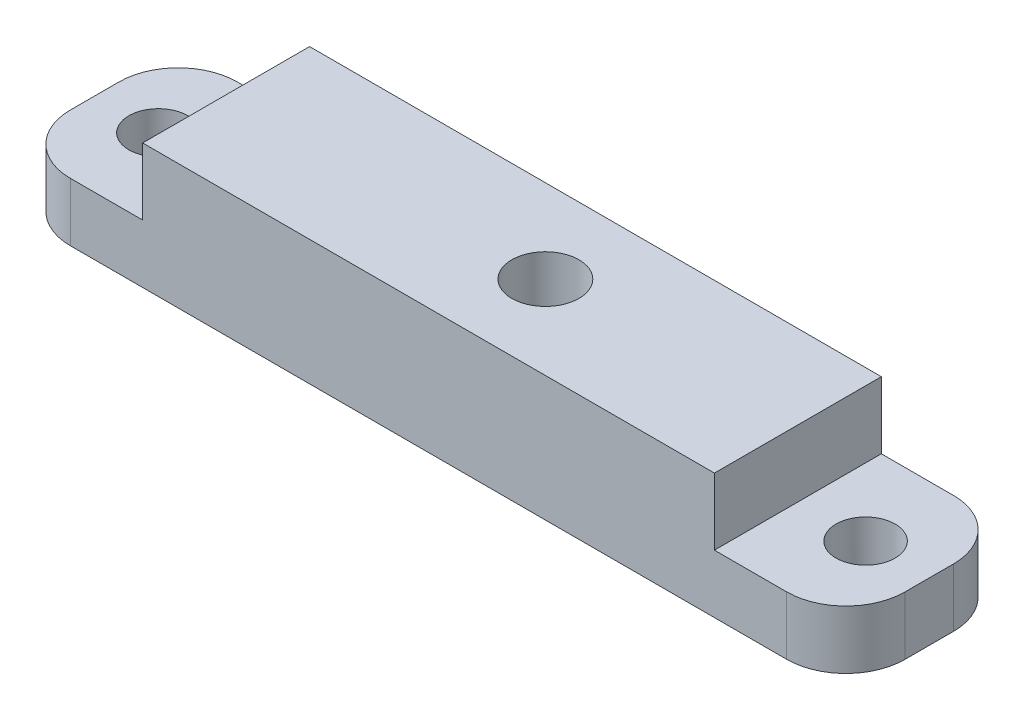
SolidWorks part; units mm, degrees
ref_plane "Front" through (0, 0, 0) normal (0, 0, 1) x (1, 0, 0)
ref_plane "Top" through (0, 0, 0) normal (0, 1, 0) x (1, 0, 0)
ref_plane "Right" through (0, 0, 0) normal (1, 0, 0) x (0, 0, -1)
sketch "Sketch1" plane through (0, 0, 0) normal (0, 1, 0) x (1, 0, 0)
  line L0 (-20.2706, 0) -> (22.1417, 0) construction
  line L1 (-31.75, 6.35) -> (31.75, 6.35)
  line L2 (-31.75, 6.35) -> (-31.75, -6.35)
  line L3 (-31.75, -6.35) -> (31.75, -6.35)
  line L4 (31.75, 6.35) -> (31.75, -6.35)
  line L5 (0, 21.9858) -> (0, -22.6095) construction
  dimension "D1" = 63.5
  dimension "D2" = 12.7
extrude "Extrude1" add sketch "Sketch1" along normal blind 9.525
hole_wizard "1/4-20 Tapped Hole1" positions "Sketch5" profile "Sketch4" tap size "1/4-20" standard "Ansi Inch" end condition through all
sketch "Sketch5" plane through (-30.8815, 9.525, 2.1316) normal (0, 1, 0) x (-1, 0, 0)
  point P0 (-33.4215, -2.1316)
  dimension "D1" = 2.54
sketch "Sketch4" plane through (2.54, 9.525, 0) normal (1, 0, 0) x (0, 0, 1)
  line L0 (0, 0) -> (0, 9.525)
  line L1 (0, 9.525) -> (2.5527, 9.525)
  line L2 (2.5527, 9.525) -> (2.5527, 0)
  line L5 (2.5527, 0) -> (0, 0)
  line L11 (0, -6.35) -> (0, 107.95) construction
  dimension "Thru Tap Drill Dia." = 5.1054
  dimension "Thru Tap Drill Depth" = 9.525
cosmetic thread "Cosmetic Thread1" parameters "D2"=6.35
hole_wizard "#8 Clearance Hole1" positions "Sketch3" profile "Sketch2" hole size "#8" standard "Ansi Inch" end condition through all
sketch "Sketch3" plane through (34.2182, 9.525, -1.2049) normal (0, 1, 0) x (-1, 0, 0)
  line L0 (34.2182, -3.1476) -> (34.2182, 3.4848) construction
  point P0 (61.1182, 1.2049)
  point P1 (7.3182, 1.2049)
  dimension "D1" = 53.8
sketch "Sketch2" plane through (-26.9, 9.525, 0) normal (1, 0, 0) x (0, 0, 1)
  line L0 (0, 0) -> (0, 9.525)
  line L1 (0, 9.525) -> (2.2479, 9.525)
  line L2 (2.2479, 9.525) -> (2.2479, 0)
  line L5 (2.2479, 0) -> (0, 0)
  line L11 (0, -6.35) -> (0, 107.95) construction
  dimension "Thru Hole Dia." = 4.4958
  dimension "Thru Hole Depth" = 9.525
sketch "Sketch6" plane through (0, 9.525, 0) normal (0, 1, 0) x (-1, 0, 0)
  line L0 (31.75, 6.35) -> (-31.75, 6.35) construction
  line L1 (31.75, -6.35) -> (21.75, -6.35)
  line L2 (31.75, -6.35) -> (31.75, 6.35)
  line L3 (31.75, 6.35) -> (21.75, 6.35)
  line L4 (21.75, -6.35) -> (21.75, 6.35)
  line L6 (-31.75, -6.35) -> (-21.75, -6.35)
  line L7 (-31.75, -6.35) -> (-31.75, 6.35)
  line L8 (-31.75, 6.35) -> (-21.75, 6.35)
  line L9 (-21.75, -6.35) -> (-21.75, 6.35)
  dimension "D1" = 10
extrude "Cut-Extrude1" cut sketch "Sketch6" against normal blind 5.08
fillet "Fillet1" radius 4.5 4 edges at (-31.75, 2.2225, -6.35) (-31.75, 2.2225, 6.35) (31.75, 2.2225, -6.35) (31.75, 2.2225, 6.35)
